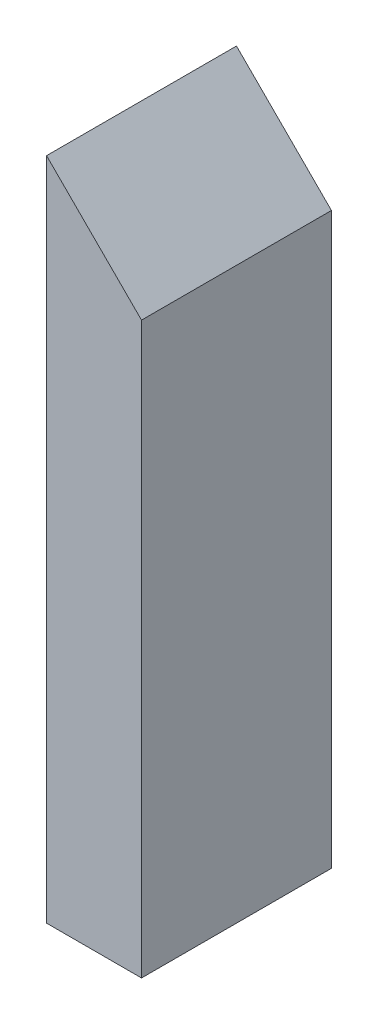
SolidWorks part; units mm, degrees
ref_plane "Piano frontale" through (0, 0, 0) normal (0, 0, 1) x (1, 0, 0)
ref_plane "Piano superiore" through (0, 0, 0) normal (0, 1, 0) x (1, 0, 0)
ref_plane "Piano destro" through (0, 0, 0) normal (1, 0, 0) x (0, 0, -1)
sketch "Schizzo1" plane through (0, 0, 0) normal (0, 0, 1) x (1, 0, 0)
  line L0 (-5, 0) -> (-5, -60)
  line L1 (-5, -60) -> (5, -60)
  line L2 (5, -60) -> (5, 0)
  line L3 (5, 0) -> (-5, 10)
  line L4 (-5, 10) -> (-5, 0)
  line L6 (-5, 10) -> (-10, 10)
  line L7 (-5, 10) -> (-5, -60)
  line L8 (-5, -60) -> (-10, -60)
  line L9 (-10, 10) -> (-10, -60)
  point P3 (0, -60)
  dimension "D1" = 70
  dimension "D2" = 10
  dimension "D3" = 10
  dimension "D4" = 5
extrude "Estrusione-Estrusione1" add sketch "Schizzo1" along normal blind 20 contours L3 L4 L0 L1 L2
